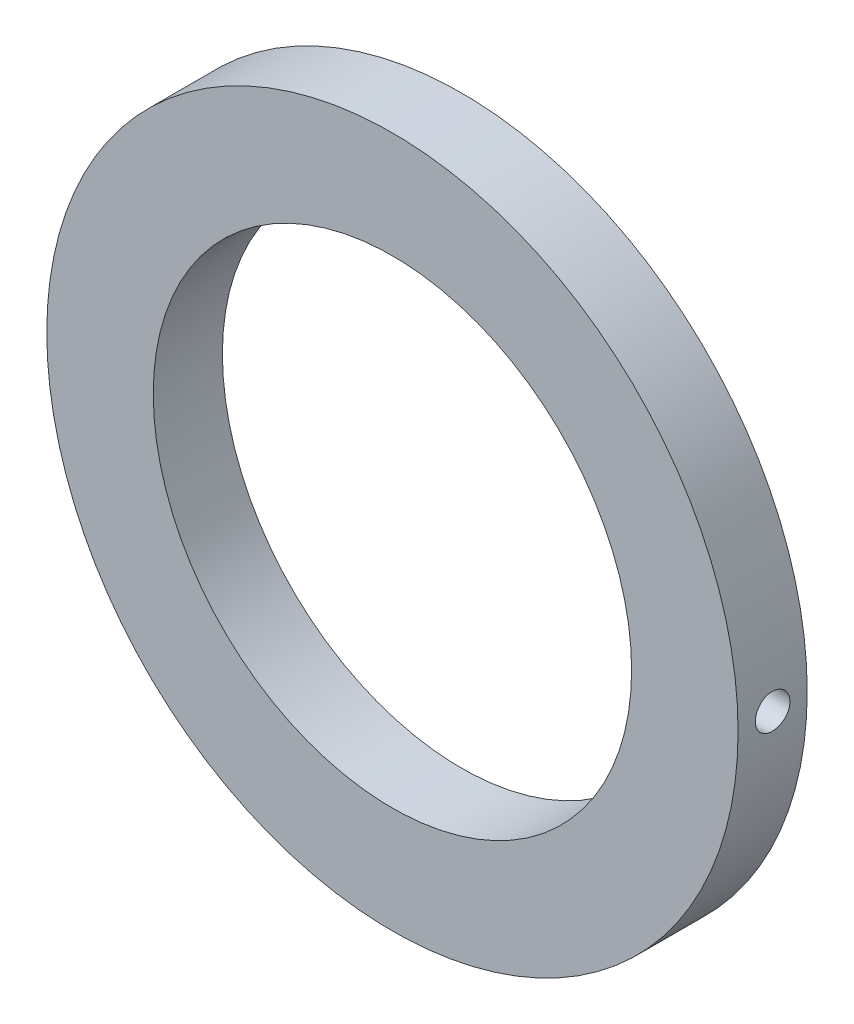
SolidWorks part; units mm, degrees
material "AISI 1020"
ref_plane "Plano frontal" through (0, 0, 0) normal (0, 0, 1) x (1, 0, 0)
ref_plane "Plano superior" through (0, 0, 0) normal (0, 1, 0) x (1, 0, 0)
ref_plane "Plano direito" through (0, 0, 0) normal (1, 0, 0) x (0, 0, -1)
sketch "Esboço1" plane through (0, 0, 0) normal (0, 0, 1) x (1, 0, 0)
  circle A0 centre (0, 0) radius 25
  circle A1 centre (0, 0) radius 17.3
  dimension "D1" = 50
  dimension "D2" = 34.6
extrude "Ressalto-extrusão1" add sketch "Esboço1" along normal blind 5
hole_wizard "Furo roscado de M3x0.51" positions "Esboço6" profile "Esboço2" tap size "M3x0.5" standard "Ansi Metric"
sketch "Esboço6" plane through (0, 0, 0) normal (1, 0, 0) x (0, 0, -1)
  line L0 (0, -25) -> (0, 25) construction
  point P0 (-2.5, 0)
  dimension "D1" = 2.5
sketch "Esboço2" plane through (0, 0, 2.5) normal (0, 1, 0) x (0, 0, 1)
  line L0 (0, 0) -> (0, 25)
  line L1 (0, 25) -> (1.25, 25)
  line L2 (1.25, 25) -> (1.25, 0)
  line L5 (1.25, 0) -> (0, 0)
  line L11 (0, -6.35) -> (0, 107.95) construction
  dimension "Thru Tap Drill Dia." = 2.5
  dimension "Thru Tap Drill Depth" = 25
cosmetic thread "Rosca de furo1" parameters "D2"=3
